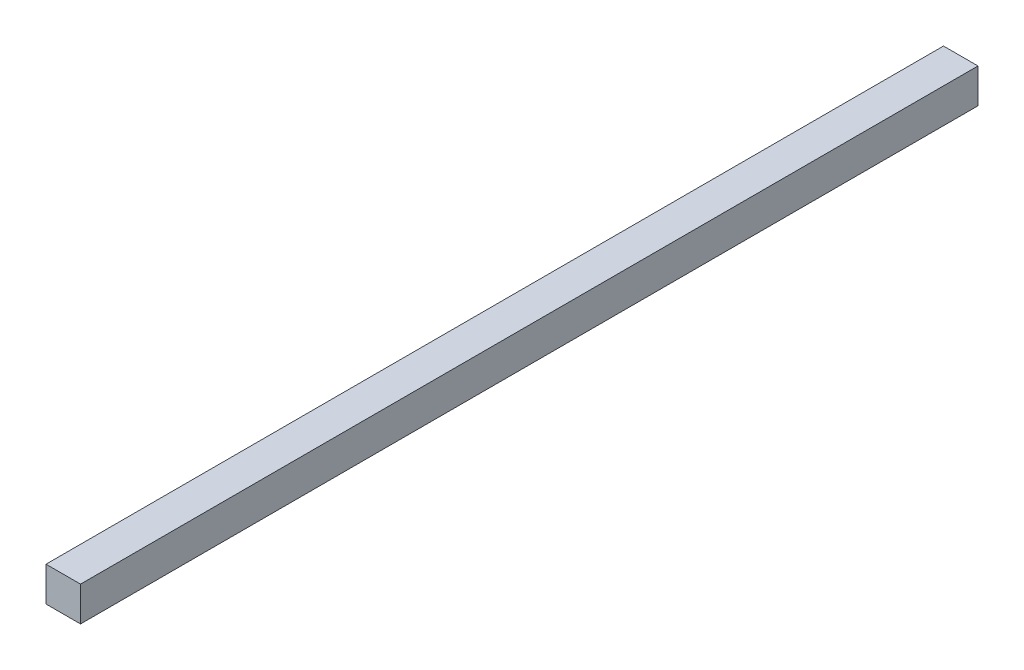
SolidWorks part; units mm, degrees
material "6061 Alloy"
ref_plane "Front Plane" through (0, 0, 0) normal (0, 0, 1) x (1, 0, 0)
ref_plane "Top Plane" through (0, 0, 0) normal (0, 1, 0) x (1, 0, 0)
ref_plane "Right Plane" through (0, 0, 0) normal (1, 0, 0) x (0, 0, -1)
sketch "Sketch1" plane through (0, 0, 0) normal (0, 0, 1) x (1, 0, 0)
  line L5 (-12.7, -12.7) -> (12.7, -12.7)
  line L6 (-12.7, -12.7) -> (-12.7, 12.7)
  line L7 (-12.7, 12.7) -> (12.7, 12.7)
  line L8 (12.7, -12.7) -> (12.7, 12.7)
  line L9 (-12.7, -12.7) -> (12.7, 12.7) construction
  line L10 (-12.7, 12.7) -> (12.7, -12.7) construction
  point P0 (0, 0)
  dimension "D1" = 25.4
  dimension "D2" = 25.4
extrude "Boss-Extrude1" add sketch "Sketch1" along normal blind 660.4
sketch "Sketch2" plane through (-12.7, 0, 0) normal (-1, 0, 0) x (0, 0, 1)
  line L0 (660.4, 12.7) -> (0, 12.7) construction
  line L1 (660.4, 12.7) -> (660.4, -12.7) construction
  line L2 (0, 0) -> (660.4, 0) construction
  line L3 (330.2, 0) -> (330.2, 66.8066) construction
  circle A0 centre (647.7, 0) radius 6.35
  circle A1 centre (12.7, 0) radius 6.35
  dimension "D1" = 12.7
  dimension "D2" = 12.7
  dimension "D3" = 12.7
extrude "Boss-Extrude2" add sketch "Sketch2" along normal blind 0.1
